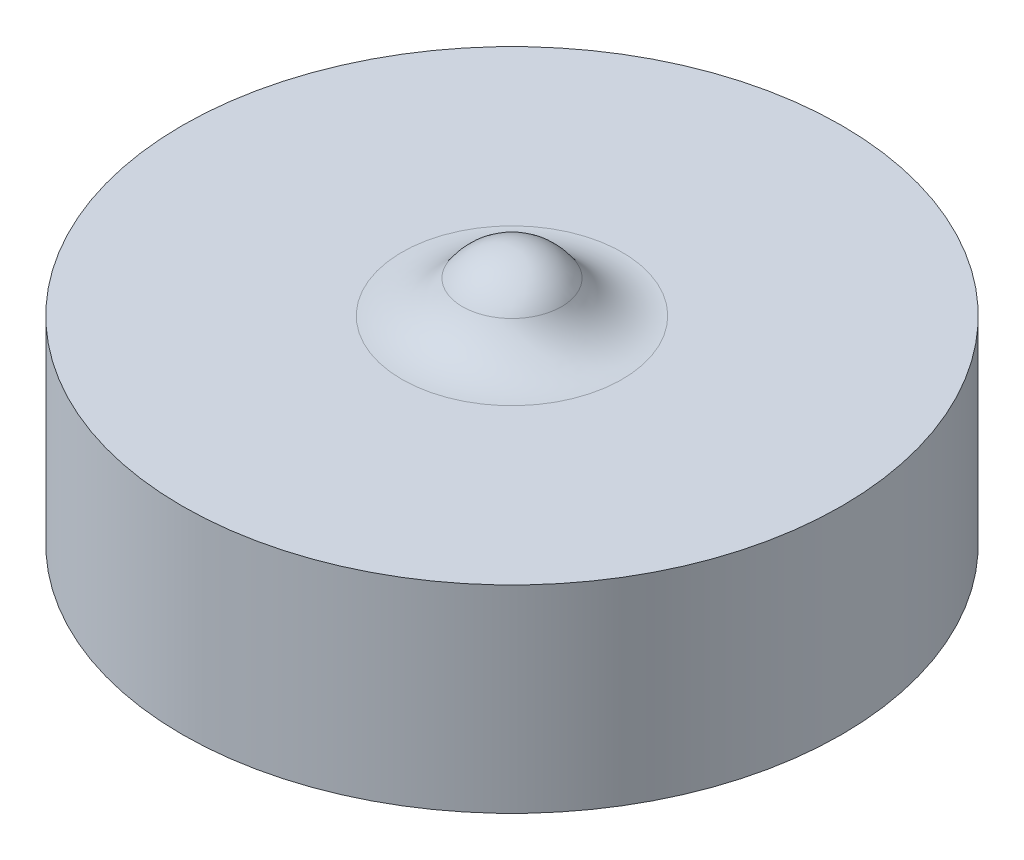
SolidWorks part; units mm, degrees
ref_plane "前视基准面" through (0, 0, 0) normal (0, 0, 1) x (1, 0, 0)
ref_plane "上视基准面" through (0, 0, 0) normal (0, 1, 0) x (1, 0, 0)
ref_plane "右视基准面" through (0, 0, 0) normal (1, 0, 0) x (0, 0, -1)
sketch "草图1" plane through (0, 0, 0) normal (0, 1, 0) x (1, 0, 0)
  circle A0 centre (0, 0) radius 5
  dimension "D1" = 10
extrude "凸台-拉伸1" add sketch "草图1" along normal blind 3
sketch "草图2" plane through (0, 0, 0) normal (0, 0, 1) x (1, 0, 0)
  line L0 (0, 0) -> (0, 3.8231) construction
  line L1 (5, 3) -> (-5, 3) construction
  line L2 (0, 3.9) -> (0, 3)
  line L3 (0, 3) -> (0.9, 3)
  arc A0 (0.9, 3) -> (0, 3.9) centre (0, 3) ccw
  dimension "D1" = 1.8
revolve "旋转1" add sketch "草图2" angle 360 about L0
fillet "圆角1" radius 1.1 1 edges at (0, 3, 0.9)
sketch "方向草图" plane through (0, 3, 0) normal (0, 1, 0) x (1, 0, 0)
  circle A0 centre (0, 0) radius 1.6703 construction
  circle A1 centre (0, 0) radius 5 construction
  circle A2 centre (0, 0) radius 1.6703
  circle A3 centre (0, 0) radius 5 construction
  point P5 (0, 0)
other "成形工具1"
